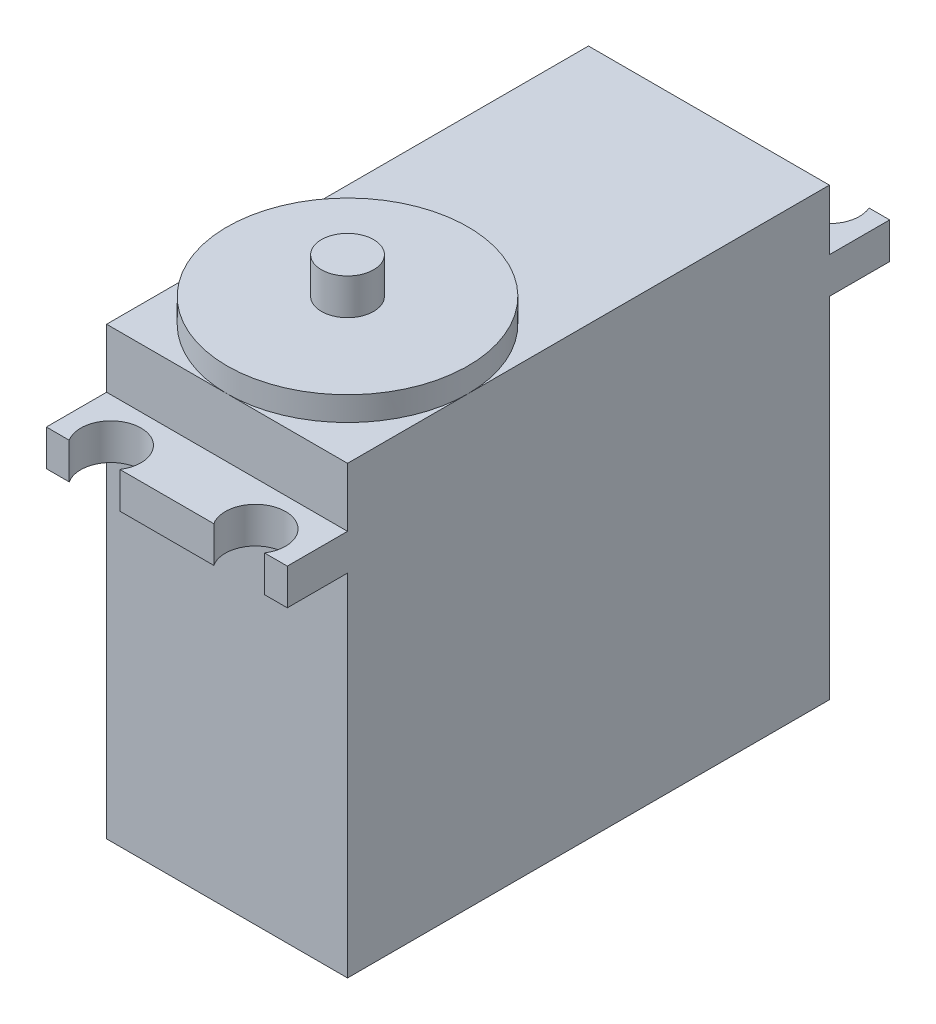
SolidWorks part; units mm, degrees
ref_plane "前视基准面" through (0, 0, 0) normal (0, 0, 1) x (1, 0, 0)
ref_plane "上视基准面" through (0, 0, 0) normal (0, 1, 0) x (1, 0, 0)
ref_plane "右视基准面" through (0, 0, 0) normal (1, 0, 0) x (0, 0, -1)
sketch "草图1" plane through (0, 0, 0) normal (0, 1, 0) x (1, 0, 0)
  line L1 (-10, 20) -> (10, 20)
  line L2 (-10, 20) -> (-10, -20)
  line L3 (-10, -20) -> (10, -20)
  line L4 (10, 20) -> (10, -20)
  point P6 (1.2624, -29.5956)
  point P7 (14.7978, 9.9099)
  point P9 (5.1402, -29.5956)
  point P11 (10, -0.4012)
  dimension "D1" = 40
  dimension "D2" = 20
  dimension "D3" = 20
  dimension "D4" = 10
extrude "凸台-拉伸1" add sketch "草图1" along normal blind 37
sketch "草图2" plane through (0, 0, 0) normal (0, 1, 0) x (1, 0, 0)
  line L0 (-10, 20) -> (-10, -20) construction
  line L1 (-9, 19) -> (9, 19) construction
  line L2 (-9, 19) -> (-9, -19) construction
  line L3 (-9, -19) -> (9, -19) construction
  line L4 (9, 19) -> (9, -19) construction
  line L5 (10, -20) -> (10, 20) construction
  line L6 (10, 20) -> (-10, 20) construction
  line L7 (-10, -20) -> (10, -20) construction
  circle A0 centre (-9, 19) radius 0.75
  circle A1 centre (9, 19) radius 0.75
  circle A2 centre (-9, -19) radius 0.75
  circle A3 centre (9, -19) radius 0.75
  dimension "D1" = 1
  dimension "D2" = 1
  dimension "D3" = 1
  dimension "D4" = 1
extrude "切除-拉伸10" cut sketch "草图2" along normal blind 2
sketch "草图3" plane through (0, 37, 0) normal (0, 1, 0) x (1, 0, 0)
  line L0 (-10, -20) -> (10, -20) construction
  circle A0 centre (0, -10) radius 10
  point P2 (0, 0)
  dimension "D1" = 20
  dimension "D2" = 10
extrude "凸台-拉伸3" add sketch "草图3" along normal blind 2 contours A0
sketch "草图4" plane through (0, 39, 0) normal (0, 1, 0) x (1, 0, 0)
  circle A0 centre (0, -10) radius 2.1674
extrude "凸台-拉伸4" add sketch "草图4" along normal blind 3
sketch "草图5" plane through (0, 0, 20) normal (0, 0, 1) x (1, 0, 0)
  line L0 (-10, 37) -> (-10, 0) construction
  line L1 (-10, 32.1104) -> (10, 32.1104)
  line L2 (-10, 32.1104) -> (-10, 29.1104)
  line L3 (-10, 29.1104) -> (10, 29.1104)
  line L4 (10, 32.1104) -> (10, 29.1104)
  line L5 (10, 37) -> (10, 0) construction
extrude "凸台-拉伸5" add sketch "草图5" along normal blind 5
sketch "草图6" plane through (0, 32.1104, 0) normal (0, 1, 0) x (1, 0, 0)
  line L0 (-10, -25) -> (-10, -20) construction
  line L1 (10, -25) -> (10, -20) construction
  circle A0 centre (-6, -23.6441) radius 2.5
  circle A1 centre (6, -23.6441) radius 2.5
  dimension "D1" = 5
  dimension "D3" = 4
  dimension "D2" = 4
sketch "草图7" plane through (0, 32.1104, 0) normal (0, 1, 0) x (1, 0, 0)
extrude "切除-拉伸13" cut sketch "草图6" against normal blind 3
sketch "草图9" plane through (0, 0, -20) normal (0, 0, -1) x (-1, 0, 0)
  line L0 (-10, 37) -> (-10, 0) construction
  line L1 (-10, 32) -> (10, 32)
  line L2 (-10, 32) -> (-10, 29)
  line L3 (-10, 29) -> (10, 29)
  line L4 (10, 32) -> (10, 29)
  line L5 (10, 37) -> (10, 0) construction
  line L6 (-10, 37) -> (10, 37) construction
  dimension "D1" = 5
  dimension "D2" = 3
extrude "凸台-拉伸7" add sketch "草图9" along normal blind 5
sketch "草图10" plane through (0, 32, 0) normal (0, 1, 0) x (1, 0, 0)
  line L0 (-10, 25) -> (-10, 20) construction
  line L1 (10, 25) -> (10, 20) construction
  line L2 (-10, 20) -> (10, 20) construction
  line L3 (10, 20) -> (-10, 20) construction
  circle A0 centre (-6, 24) radius 2.5
  circle A1 centre (6, 24) radius 2.5
  point P2 (0, 0)
  point P5 (6.1889, 23.0021)
  dimension "D2" = 4
  dimension "D4" = 4
  dimension "D5" = 5
  dimension "D6" = 5
  dimension "D1" = 4
  dimension "D3" = 4
extrude "切除-拉伸14" cut sketch "草图10" against normal blind 3
